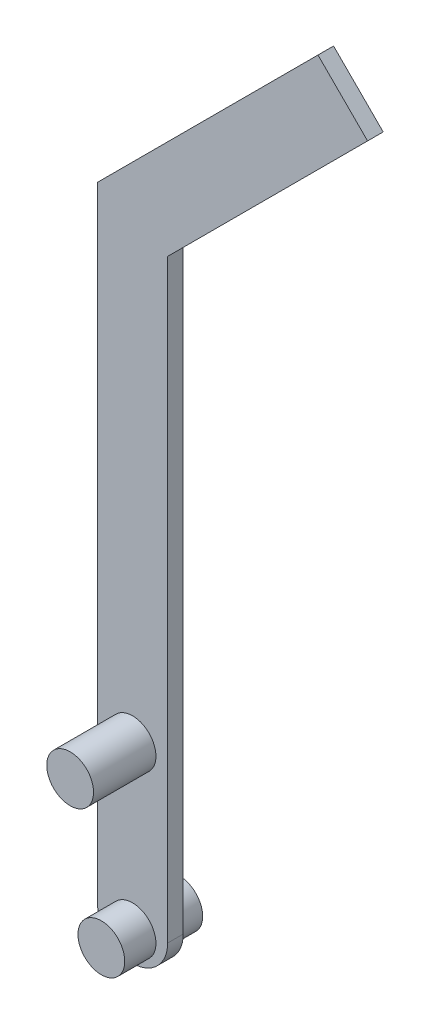
SolidWorks part; units mm, degrees
ref_plane "前视基准面" through (0, 0, 0) normal (0, 0, 1) x (1, 0, 0)
ref_plane "上视基准面" through (0, 0, 0) normal (0, 1, 0) x (1, 0, 0)
ref_plane "右视基准面" through (0, 0, 0) normal (1, 0, 0) x (0, 0, -1)
other "Configuration Table"
sketch "草图1" plane through (0, 0, 0) normal (0, 0, 1) x (1, 0, 0)
  line L0 (0, -20) -> (0, 20) construction
  line L1 (-4.5, -20) -> (-4.5, 20)
  line L2 (4.5, -20) -> (4.5, 20)
  arc A0 (-4.5, -20) -> (4.5, -20) centre (0, -20) ccw
  arc A1 (4.5, 20) -> (-4.5, 20) centre (0, 20) ccw
  point P2 (0, 0)
extrude "凸台-拉伸1" add sketch "草图1" along normal blind 2
sketch "草图2" plane through (0, 0, 2) normal (0, 0, 1) x (1, 0, 0)
  circle A0 centre (0, 0) radius 3
extrude "凸台-拉伸2" add sketch "草图2" along normal blind 8
sketch "草图3" plane through (0, 0, 2) normal (0, 0, 1) x (1, 0, 0)
  circle A0 centre (0, -20.775) radius 3
extrude "凸台-拉伸3" add sketch "草图3" along normal blind 4 and the other way blind 6
sketch "草图4" plane through (0, 0, 2) normal (0, 0, 1) x (1, 0, 0)
  line L0 (-4.5, 60) -> (-4.5, 20)
  line L1 (-4.5, 60) -> (23.7843, 88.2843)
  line L2 (23.7843, 88.2843) -> (30.1482, 81.9203)
  line L3 (-4.5, 20) -> (-4.5, -20) construction
  line L4 (4.5, 20) -> (4.5, 56.2721)
  line L5 (4.5, 56.2721) -> (30.1482, 81.9203)
  line L6 (-4.5, 20) -> (4.5, 20)
  arc A2 (4.5, 20) -> (-4.5, 20) centre (0, 20) ccw construction
  dimension "D1" = 135
  dimension "D2" = 135
  dimension "D3" = 40
  dimension "D4" = 40
extrude "凸台-拉伸4" add sketch "草图4" against normal blind 2
scale "缩放比例3" scale about centroid uniform scaling yes scale factor 3.5
